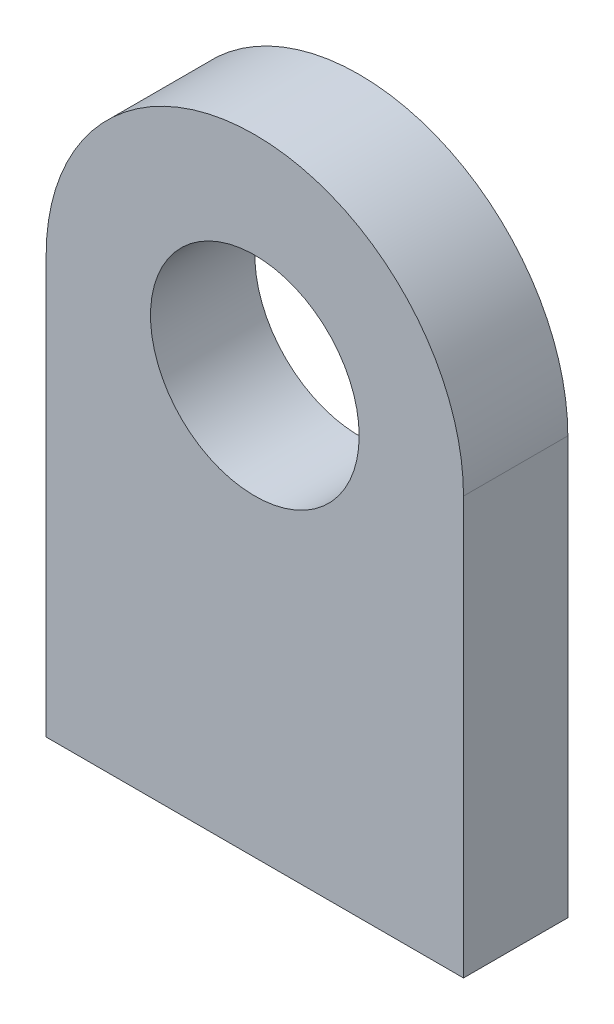
SolidWorks part; units mm, degrees
ref_plane "Front Plane" through (0, 0, 0) normal (0, 0, 1) x (1, 0, 0)
ref_plane "Top Plane" through (0, 0, 0) normal (0, 1, 0) x (1, 0, 0)
ref_plane "Right Plane" through (0, 0, 0) normal (1, 0, 0) x (0, 0, -1)
sketch "Sketch1" plane through (0, 0, 0) normal (0, 0, 1) x (1, 0, 0)
  line L1 (6.35, -6.35) -> (-6.35, -6.35)
  line L2 (6.35, -6.35) -> (6.35, 6.35)
  line L4 (-6.35, -6.35) -> (-6.35, 6.35)
  line L5 (6.35, -6.35) -> (-6.35, 6.35) construction
  line L6 (6.35, 6.35) -> (-6.35, -6.35) construction
  arc A0 (-6.35, 6.35) -> (6.35, 6.35) centre (0, 6.35) cw
  circle A1 centre (0, 6.35) radius 3.175
  point P0 (0, 0)
  dimension "D2" = 6.35
  dimension "D1" = 12.7
extrude "Boss-Extrude1" add sketch "Sketch1" along normal blind 3.175
